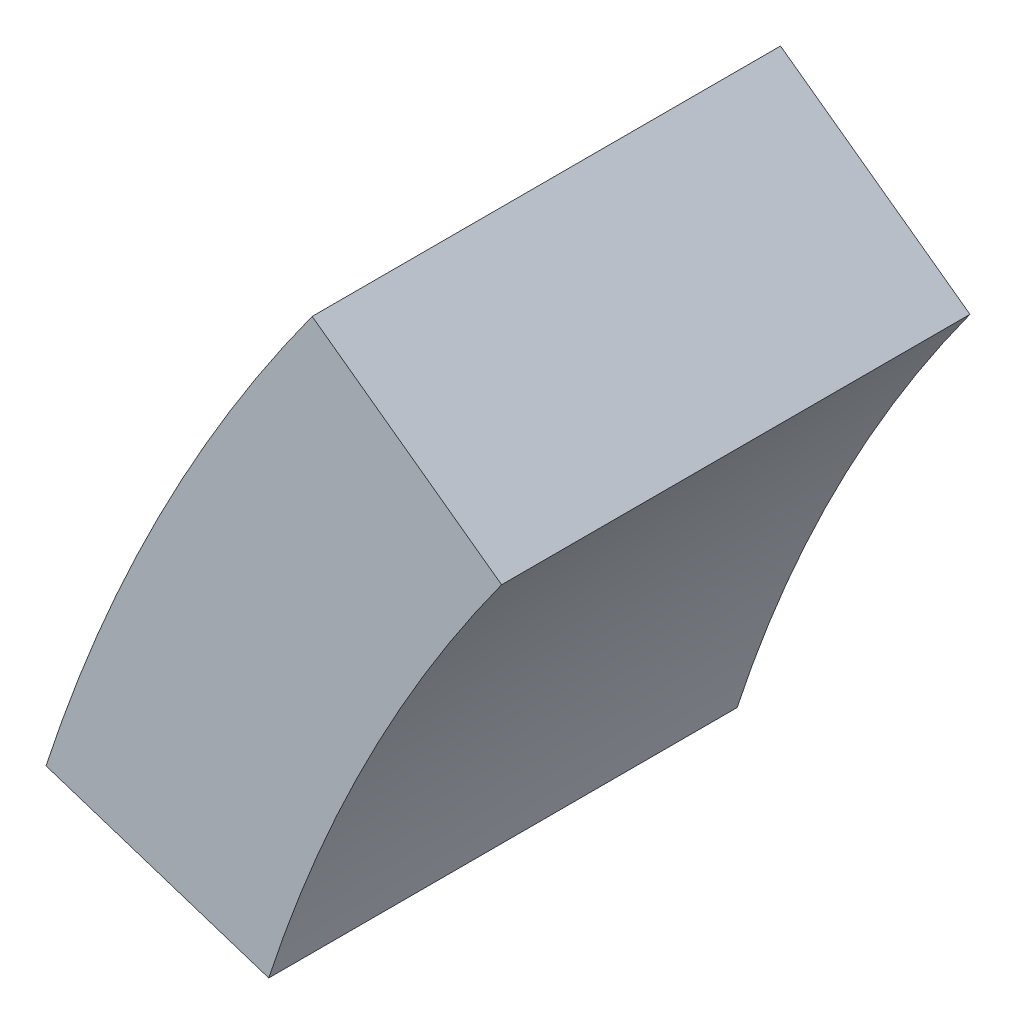
SolidWorks part; units mm, degrees
material "砖"
ref_plane "前视基准面" through (0, 0, 0) normal (0, 0, 1) x (1, 0, 0)
ref_plane "上视基准面" through (0, 0, 0) normal (0, 1, 0) x (1, 0, 0)
ref_plane "右视基准面" through (0, 0, 0) normal (1, 0, 0) x (0, 0, -1)
sketch "草图1" plane through (0, 0, 0) normal (0, 0, 1) x (1, 0, 0)
  line L0 (-4560, 0) -> (-7920, 0)
  line L1 (-12480, 7680) -> (0, 7680)
  line L2 (-12480, 7680) -> (-12480, 0)
  line L3 (-12480, 0) -> (0, 0)
  line L4 (0, 7680) -> (0, 0)
  line L5 (-7920, 0) -> (-7920, 3840)
  line L6 (-7920, 3840) -> (-4560, 3840)
  line L7 (-4560, 3840) -> (-4560, 0)
  line L8 (-7920, 3840) -> (-8160, 3840)
  line L9 (-4560, 3840) -> (-4320, 3840)
  line L10 (-7837.7749, 4359.1486) -> (-8066.0285, 4433.3126)
  line L11 (-7599.1486, 4827.4792) -> (-7793.3126, 4968.5477)
  line L12 (-7227.4792, 5199.1486) -> (-7368.5477, 5393.3126)
  line L13 (-6759.1486, 5437.7749) -> (-6833.3126, 5666.0285)
  line L14 (-6240, 5520) -> (-6240, 5760)
  line L15 (-5720.8514, 5437.7749) -> (-5646.6874, 5666.0285)
  line L16 (-5252.5208, 5199.1486) -> (-5111.4523, 5393.3126)
  line L17 (-4880.8514, 4827.4792) -> (-4686.6874, 4968.5477)
  line L18 (-4642.2251, 4359.1486) -> (-4413.9715, 4433.3126)
  line L19 (-4560, 3840) -> (-4320, 3840)
  line L20 (-4573.7633, 3298.6069) -> (-4560, 3294.1349)
  line L21 (-6833.3126, 5666.0285) -> (-6928.8298, 5960)
  line L22 (-5683.7694, 5551.9017) -> (-5551.1702, 5960)
  line L23 (-5551.1702, 5960) -> (-6928.8298, 5960)
  line L24 (-7920, 0) -> (-9123.3069, 0)
  line L25 (-8160, 0) -> (-8640, 0)
  line L26 (-8160, 0) -> (-8640, 0)
  line L27 (-8640, 3840) -> (-8160, 3840)
  line L28 (-8640, 3840) -> (-8640, 4264)
  line L29 (-7837.7749, 3320.8514) -> (-7920, 3294.1349) [skipped]
  line L30 (-7599.1486, 2852.5208) -> (-7793.3126, 2711.4523) [skipped]
  line L31 (-7227.4792, 2480.8514) -> (-7368.5477, 2286.6874) [skipped]
  line L32 (-6759.1486, 2242.2251) -> (-6833.3126, 2013.9715) [skipped]
  line L33 (-6240, 2160) -> (-6240, 1920) [skipped]
  line L34 (-5720.8514, 2242.2251) -> (-5646.6874, 2013.9715) [skipped]
  line L35 (-5252.5208, 2480.8514) -> (-5111.4523, 2286.6874) [skipped]
  line L36 (-4880.8514, 2852.5208) -> (-4686.6874, 2711.4523) [skipped]
  line L37 (-8640, 4264) -> (-8112.5982, 4264)
  line L38 (-8112.5982, 4264) -> (-8592.5982, 4264)
  line L39 (-8592.5982, 4264) -> (-8592.5982, 4688)
  line L40 (-8592.5982, 4688) -> (-7962.5841, 4688)
  line L41 (-7962.5841, 4688) -> (-8442.5841, 4688)
  line L42 (-8442.5841, 4688) -> (-8442.5841, 5112)
  line L43 (-8442.5841, 5112) -> (-7678.1989, 5112)
  line L44 (-7678.1989, 5112) -> (-8158.1989, 5112)
  line L45 (-8158.1989, 5112) -> (-8158.1989, 5536)
  line L46 (-8158.1989, 5536) -> (-7139.9911, 5536)
  line L47 (-7139.9911, 5536) -> (-7619.9911, 5536)
  line L48 (-7619.9911, 5536) -> (-7619.9911, 5960)
  line L49 (-7619.9911, 5960) -> (-6928.8298, 5960)
  arc A0 (-4560, 3840) -> (-7920, 3840) centre (-6240, 3840) ccw
  arc A1 (-4320, 3840) -> (-8160, 3840) centre (-6240, 3840) ccw
  point P7 (-6240, 0)
  point P56 (-6240, 3840)
  dimension "D5" = 3840
  dimension "D1" = 12480
  dimension "D2" = 7680
  dimension "D3" = 3360
  dimension "D4" = 3840
  dimension "D7" = 240
  dimension "D8" = 480
  dimension "D9" = 424
  dimension "D10" = 720
  dimension "D11" = 480
  dimension "D12" = 480
  dimension "D13" = 480
  dimension "D14" = 480
  dimension "D6" = 20
extrude "凸台-拉伸1" add sketch "草图1" along normal blind 480 contours L11 A1 L10 A0
scale "缩放比例1" scale about origin uniform scaling yes scale factor 1.3
